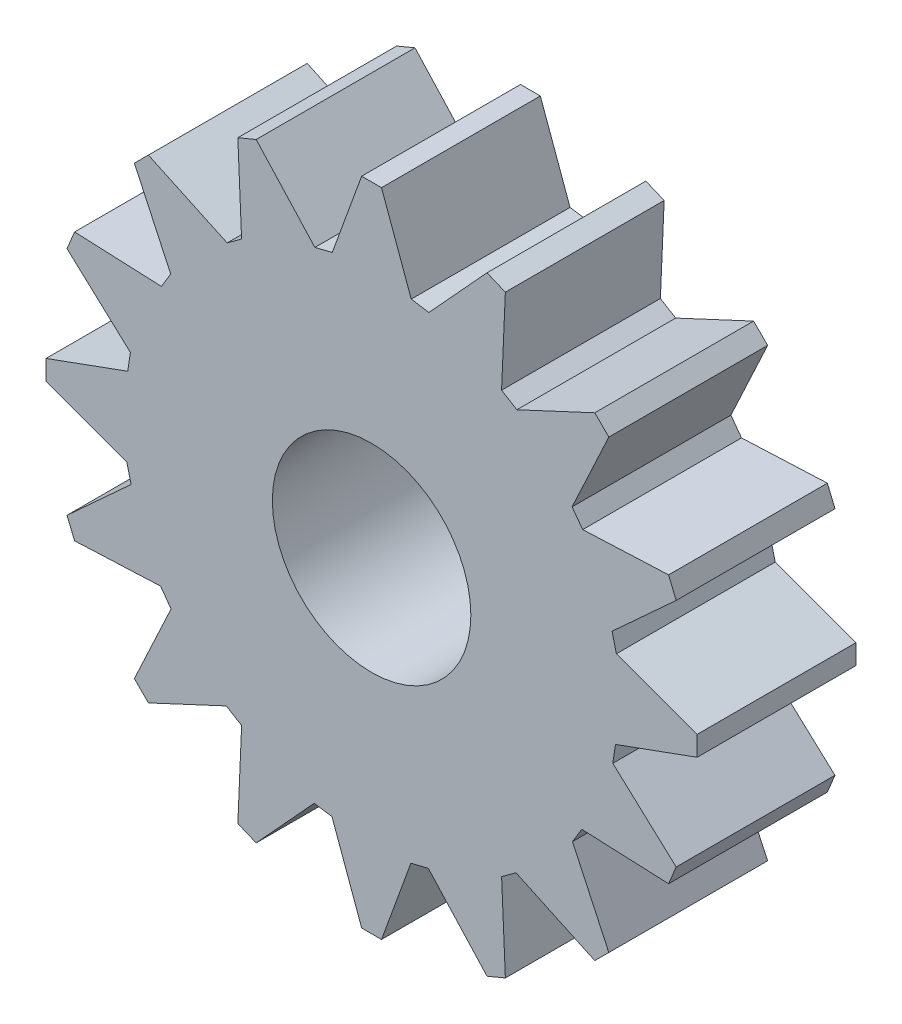
SolidWorks part; units mm, degrees
ref_plane "前视基准面" through (0, 0, 0) normal (0, 0, 1) x (1, 0, 0)
ref_plane "上视基准面" through (0, 0, 0) normal (0, 1, 0) x (1, 0, 0)
ref_plane "右视基准面" through (0, 0, 0) normal (1, 0, 0) x (0, 0, -1)
sketch "草图1" plane through (0, 0, 0) normal (0, 0, 1) x (1, 0, 0)
  line L0 (-0.25, 8.2) -> (0.25, 8.2)
  line L1 (0.25, 8.2) -> (0.9986, 6.1431)
  line L2 (-0.25, 8.2) -> (-0.9905, 6.1656)
  line L3 (3.369, 7.4801) -> (3.2735, 5.2933)
  line L4 (2.907, 7.6715) -> (3.369, 7.4801)
  line L5 (2.907, 7.6715) -> (1.4444, 6.0753)
  line L6 (5.9751, 5.6215) -> (5.05, 3.6377)
  line L7 (5.6215, 5.9751) -> (5.9751, 5.6215)
  line L8 (5.6215, 5.9751) -> (3.6594, 5.0601)
  line L9 (7.6715, 2.907) -> (6.0577, 1.4282)
  line L10 (7.4801, 3.369) -> (7.6715, 2.907)
  line L11 (7.4801, 3.369) -> (5.3172, 3.2745)
  line L12 (8.2, -0.25) -> (6.1431, -0.9986)
  line L13 (8.2, 0.25) -> (8.2, -0.25)
  line L14 (8.2, 0.25) -> (6.1656, 0.9905)
  line L15 (7.4801, -3.369) -> (5.2933, -3.2735)
  line L16 (7.6715, -2.907) -> (7.4801, -3.369)
  line L17 (7.6715, -2.907) -> (6.0753, -1.4444)
  line L18 (5.6215, -5.9751) -> (3.6377, -5.05)
  line L19 (5.9751, -5.6215) -> (5.6215, -5.9751)
  line L20 (5.9751, -5.6215) -> (5.0601, -3.6594)
  line L21 (2.907, -7.6715) -> (1.4282, -6.0577)
  line L22 (3.369, -7.4801) -> (2.907, -7.6715)
  line L23 (3.369, -7.4801) -> (3.2745, -5.3172)
  line L24 (-0.25, -8.2) -> (-0.9986, -6.1431)
  line L25 (0.25, -8.2) -> (-0.25, -8.2)
  line L26 (0.25, -8.2) -> (0.9905, -6.1656)
  line L27 (-3.369, -7.4801) -> (-3.2735, -5.2933)
  line L28 (-2.907, -7.6715) -> (-3.369, -7.4801)
  line L29 (-2.907, -7.6715) -> (-1.4444, -6.0753)
  line L30 (-5.9751, -5.6215) -> (-5.05, -3.6377)
  line L31 (-5.6215, -5.9751) -> (-5.9751, -5.6215)
  line L32 (-5.6215, -5.9751) -> (-3.6594, -5.0601)
  line L33 (-7.6715, -2.907) -> (-6.0577, -1.4282)
  line L34 (-7.4801, -3.369) -> (-7.6715, -2.907)
  line L35 (-7.4801, -3.369) -> (-5.3172, -3.2745)
  line L36 (-8.2, 0.25) -> (-6.1431, 0.9986)
  line L37 (-8.2, -0.25) -> (-8.2, 0.25)
  line L38 (-8.2, -0.25) -> (-6.1656, -0.9905)
  line L39 (-7.4801, 3.369) -> (-5.2933, 3.2735)
  line L40 (-7.6715, 2.907) -> (-7.4801, 3.369)
  line L41 (-7.6715, 2.907) -> (-6.0753, 1.4444)
  line L42 (-5.6215, 5.9751) -> (-3.6377, 5.05)
  line L43 (-5.9751, 5.6215) -> (-5.6215, 5.9751)
  line L44 (-5.9751, 5.6215) -> (-5.0601, 3.6594)
  line L45 (-2.907, 7.6715) -> (-1.4282, 6.0577)
  line L46 (-3.369, 7.4801) -> (-2.907, 7.6715)
  line L47 (-3.369, 7.4801) -> (-3.2745, 5.3172)
  line L48 (-0.9905, 6.1656) -> (-1.4282, 6.0577)
  line L49 (1.4444, 6.0753) -> (0.9986, 6.1431)
  line L50 (3.6594, 5.0601) -> (3.2735, 5.2933)
  line L51 (5.3172, 3.2745) -> (5.05, 3.6377)
  line L52 (6.1656, 0.9905) -> (6.0577, 1.4282)
  line L53 (6.0753, -1.4444) -> (6.1431, -0.9986)
  line L54 (5.0601, -3.6594) -> (5.2933, -3.2735)
  line L55 (3.2745, -5.3172) -> (3.6377, -5.05)
  line L56 (0.9905, -6.1656) -> (1.4282, -6.0577)
  line L57 (-1.4444, -6.0753) -> (-0.9986, -6.1431)
  line L58 (-3.6594, -5.0601) -> (-3.2735, -5.2933)
  line L59 (-5.3172, -3.2745) -> (-5.05, -3.6377)
  line L60 (-6.1656, -0.9905) -> (-6.0577, -1.4282)
  line L61 (-6.0753, 1.4444) -> (-6.1431, 0.9986)
  line L62 (-5.0601, 3.6594) -> (-5.2933, 3.2735)
  line L63 (-3.2745, 5.3172) -> (-3.6377, 5.05)
  line L64 (0, 0) -> (9.3919, 4.5608) construction
  circle A0 centre (0, 0) radius 2.5
  point P7 (0, 8.2)
  point P72 (0, 0)
  point P104 (0, 0)
  dimension "D1" = 5
  dimension "D3" = 0.5
  dimension "D4" = 70
  dimension "D5" = 70
  dimension "D6" = 8.2
  dimension "D7" = 16
extrude "凸台-拉伸1" add sketch "草图1" along normal blind 4
